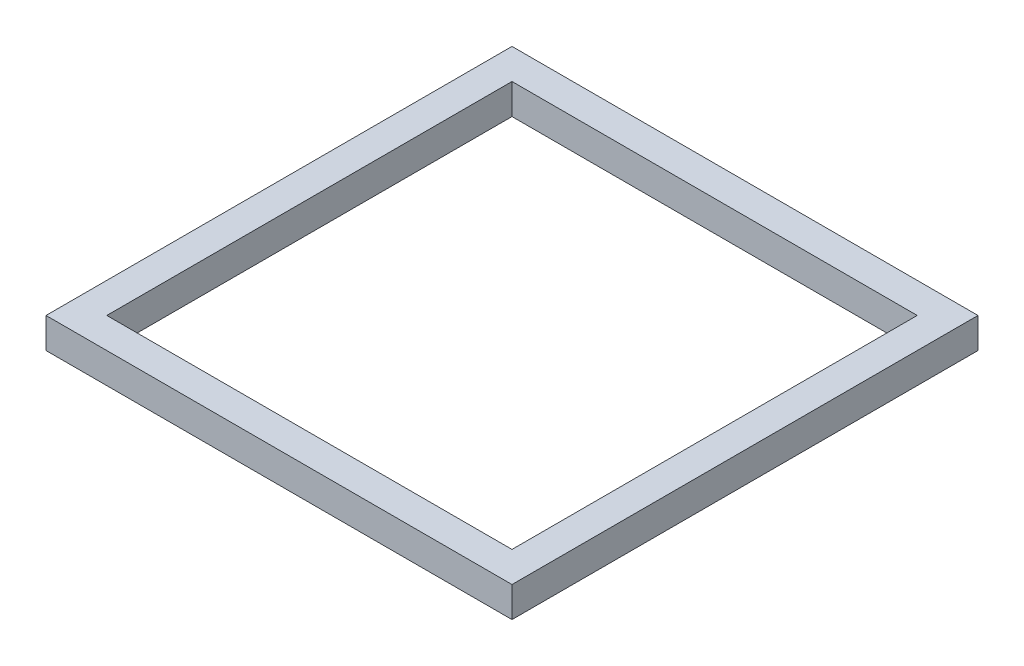
SolidWorks part; units mm, degrees
ref_plane "Alzado" through (0, 0, 0) normal (0, 0, 1) x (1, 0, 0)
ref_plane "Planta" through (0, 0, 0) normal (0, 1, 0) x (1, 0, 0)
ref_plane "Vista lateral" through (0, 0, 0) normal (1, 0, 0) x (0, 0, -1)
sketch "Croquis1" plane through (0, 0, 0) normal (0, 1, 0) x (1, 0, 0)
  line L1 (-23, -23) -> (23, -23)
  line L2 (-23, -23) -> (-23, 23)
  line L3 (-23, 23) -> (23, 23)
  line L4 (23, -23) -> (23, 23)
  line L5 (-23, -23) -> (23, 23) construction
  line L6 (-23, 23) -> (23, -23) construction
  line L7 (20, -20) -> (-20, -20)
  line L8 (20, -20) -> (20, 20)
  line L9 (20, 20) -> (-20, 20)
  line L10 (-20, -20) -> (-20, 20)
  line L11 (20, -20) -> (-20, 20) construction
  line L12 (20, 20) -> (-20, -20) construction
  point P0 (0, 0)
  point P6 (0, 0)
  dimension "D1" = 46
  dimension "D2" = 46
  dimension "D3" = 40
  dimension "D4" = 40
extrude "Saliente-Extruir1" add sketch "Croquis1" along normal blind 3
